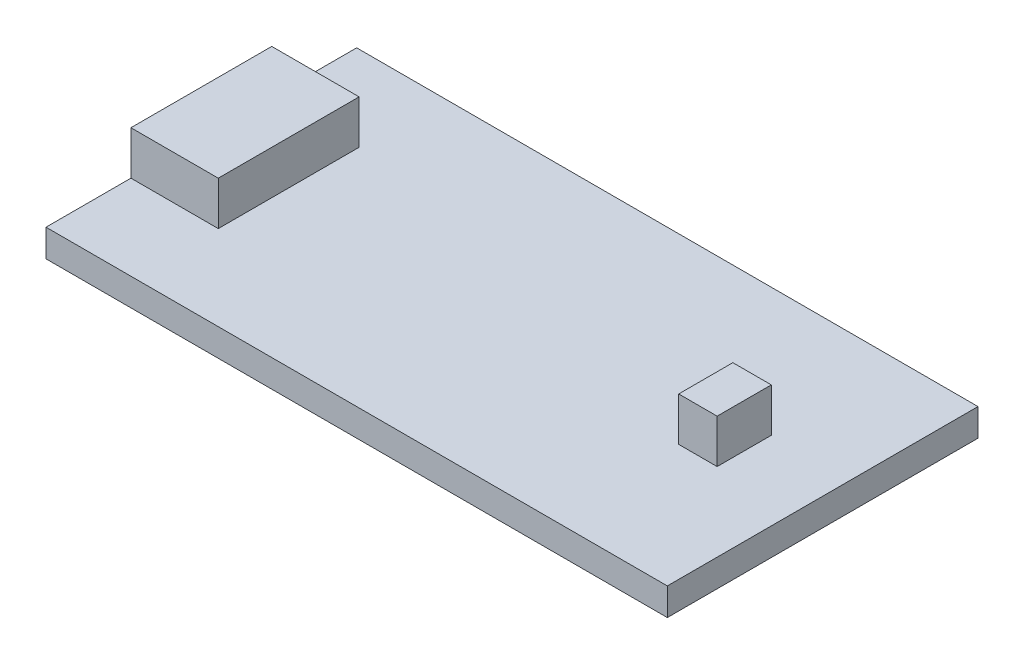
SolidWorks part; units mm, degrees
ref_plane "Front Plane" through (0, 0, 0) normal (0, 0, 1) x (1, 0, 0)
ref_plane "Top Plane" through (0, 0, 0) normal (0, 1, 0) x (1, 0, 0)
ref_plane "Right Plane" through (0, 0, 0) normal (1, 0, 0) x (0, 0, -1)
sketch "Sketch1" plane through (0, 0, 0) normal (0, 1, 0) x (1, 0, 0)
  line L1 (-17.78, 8.89) -> (17.78, 8.89)
  line L2 (-17.78, 8.89) -> (-17.78, -8.89)
  line L3 (-17.78, -8.89) -> (17.78, -8.89)
  line L4 (17.78, 8.89) -> (17.78, -8.89)
  line L5 (0, -8.89) -> (0, 8.89) construction
  line L6 (-17.78, 0) -> (17.78, 0) construction
  point P0 (0, 0)
  dimension "D1" = 35.56
  dimension "D2" = 17.78
extrude "Board" add sketch "Sketch1" along normal blind 1.57
sketch "Sketch2" plane through (0, 1.57, 0) normal (0, 1, 0) x (1, 0, 0)
  line L0 (-17.78, 8.89) -> (-17.78, -8.89) construction
  line L1 (-17.78, -4.03) -> (-12.78, -4.03)
  line L2 (-17.78, -4.03) -> (-17.78, 4.03)
  line L3 (-17.78, 4.03) -> (-12.78, 4.03)
  line L4 (-12.78, -4.03) -> (-12.78, 4.03)
  line L5 (-15.28, 4.03) -> (-15.28, -4.03) construction
  line L6 (-17.78, 0) -> (-12.78, 0) construction
  point P0 (-15.28, 0)
  dimension "D1" = 8.06
  dimension "D2" = 5
extrude "MicroUSB" add sketch "Sketch2" along normal blind 2.5
sketch "Sketch3" plane through (0, 1.57, 0) normal (0, 1, 0) x (1, 0, 0)
  line L0 (-17.78, 8.89) -> (-17.78, 4.03) construction
  line L1 (11.09, -1.55) -> (13.29, -1.55)
  line L2 (11.09, -1.55) -> (11.09, 1.55)
  line L3 (11.09, 1.55) -> (13.29, 1.55)
  line L4 (13.29, -1.55) -> (13.29, 1.55)
  line L5 (12.19, 1.55) -> (12.19, -1.55) construction
  line L6 (11.09, 0) -> (13.29, 0) construction
  point P0 (12.19, 0)
  dimension "D1" = 3.1
  dimension "D2" = 29.97
  dimension "D3" = 2.2
extrude "Button" add sketch "Sketch3" along normal blind 2.5
